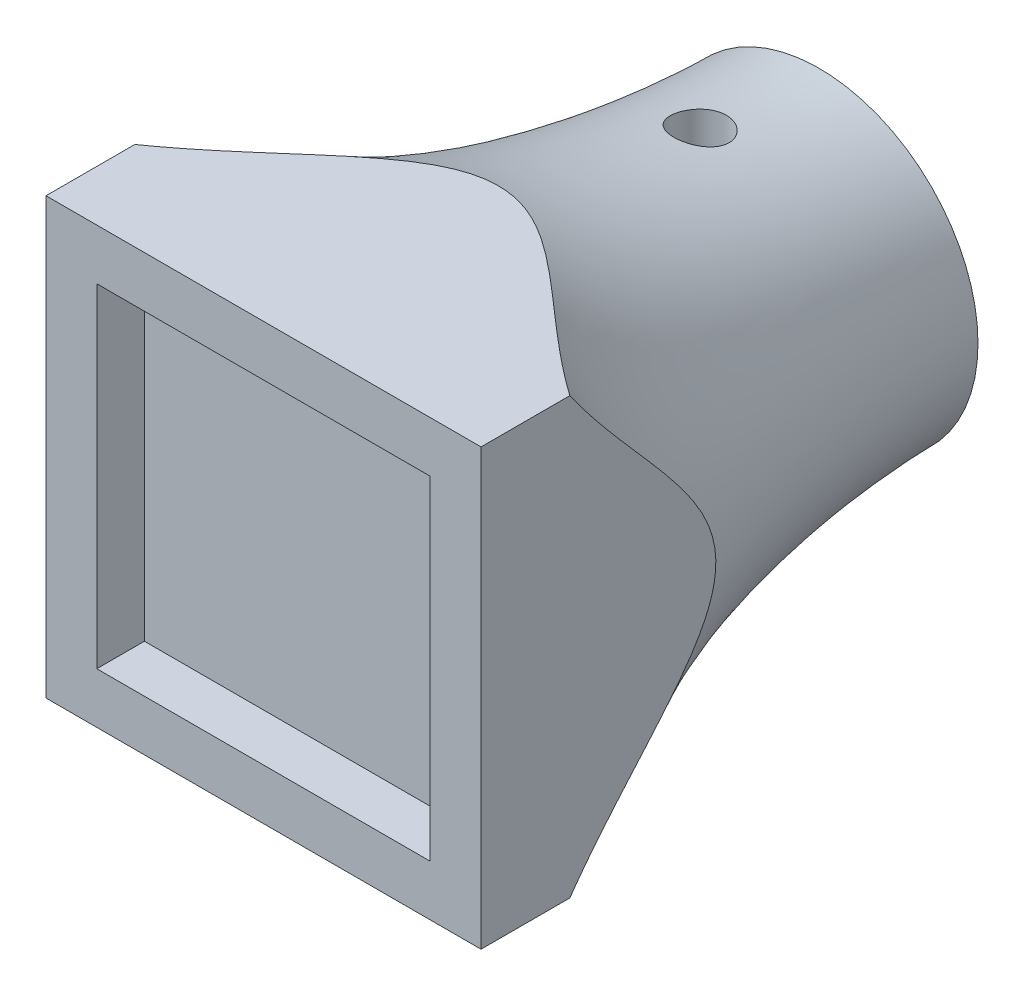
SolidWorks part; units mm, degrees
ref_plane "Front Plane" through (0, 0, 0) normal (0, 0, 1) x (1, 0, 0)
ref_plane "Top Plane" through (0, 0, 0) normal (0, 1, 0) x (1, 0, 0)
ref_plane "Right Plane" through (0, 0, 0) normal (1, 0, 0) x (0, 0, -1)
sketch "Sketch1" plane through (0, 0, 0) normal (0, 0, 1) x (1, 0, 0)
  circle A0 centre (0, 0) radius 10
  dimension "D1" = 20
extrude "Boss-Extrude1" add sketch "Sketch1" along normal blind 30
sketch "Sketch2" plane through (0, 0, 30) normal (0, 0, 1) x (1, 0, 0)
  line L0 (13.7, 13.7) -> (-13.7, 13.7)
  line L1 (10.5, 10.5) -> (-10.5, 10.5) construction
  line L2 (10.5, 10.5) -> (10.5, -10.5) construction
  line L3 (10.5, -10.5) -> (-10.5, -10.5) construction
  line L4 (-10.5, 10.5) -> (-10.5, -10.5) construction
  line L5 (10.5, 10.5) -> (-10.5, -10.5) construction
  line L6 (10.5, -10.5) -> (-10.5, 10.5) construction
  line L7 (-13.7, 13.7) -> (-13.7, -13.7)
  line L8 (13.7, -13.7) -> (-13.7, -13.7)
  line L9 (13.7, 13.7) -> (13.7, -13.7)
  point P0 (0, 0)
  dimension "D1" = 21
  dimension "D2" = 21
  dimension "D3" = 3.2
extrude "Boss-Extrude2" add sketch "Sketch2" along normal blind 5
sketch "Sketch3" plane through (0, 0, 35) normal (0, 0, 1) x (1, 0, 0)
  line L1 (10.5, 10.5) -> (-10.5, 10.5)
  line L2 (10.5, 10.5) -> (10.5, -10.5)
  line L3 (10.5, -10.5) -> (-10.5, -10.5)
  line L4 (-10.5, 10.5) -> (-10.5, -10.5)
  line L5 (10.5, 10.5) -> (-10.5, -10.5) construction
  line L6 (10.5, -10.5) -> (-10.5, 10.5) construction
  point P0 (0, 0)
  dimension "D1" = 21
  dimension "D2" = 21
extrude "Cut-Extrude1" cut sketch "Sketch3" against normal blind 3
sketch "Sketch5" plane through (0, 0, 0) normal (1, 0, 0) x (0, 0, -1)
  line L0 (-63.5412, 0) -> (-78.0067, 0)
sketch "Sketch6" plane through (0, 0, 0) normal (1, 0, 0) x (0, 0, -1)
  line L0 (-30, 0) -> (-30, 20)
  line L1 (-30, -13.7) -> (-30, 13.7) construction
  line L2 (-30, 0) -> (0, 0)
  line L3 (0, 0) -> (0, 10)
  line L4 (18.8276, 10) -> (-18.8276, 10) construction
  spline S0 degree 3 poles (-30, 20) (-22.0999, 11.2486) (-4.6132, 10) (0, 10) knots 0 0 0 0 1 1 1 1
  dimension "D1" = 20
revolve "Revolve1" add sketch "Sketch6" angle 360 about L0
sketch "Sketch7" plane through (0, 0, 30) normal (0, 0, 1) x (1, 0, 0)
  line L1 (13.7, 13.7) -> (-13.7, 13.7)
  line L2 (13.7, 13.7) -> (13.7, -13.7)
  line L3 (13.7, -13.7) -> (-13.7, -13.7)
  line L4 (-13.7, 13.7) -> (-13.7, -13.7)
  line L5 (13.7, 13.7) -> (-13.7, -13.7) construction
  line L6 (13.7, -13.7) -> (-13.7, 13.7) construction
  line L7 (23.5697, 23.5697) -> (-23.5697, 23.5697)
  line L8 (23.5697, 23.5697) -> (23.5697, -23.5697)
  line L9 (23.5697, -23.5697) -> (-23.5697, -23.5697)
  line L10 (-23.5697, 23.5697) -> (-23.5697, -23.5697)
  line L11 (23.5697, 23.5697) -> (-23.5697, -23.5697) construction
  line L12 (23.5697, -23.5697) -> (-23.5697, 23.5697) construction
  point P0 (0, 0)
  point P7 (0, 0)
extrude "Cut-Extrude2" cut sketch "Sketch7" against normal blind 78
sketch "Sketch8" plane through (0, 0, 0) normal (0, 0, -1) x (-1, 0, 0)
  line L0 (-1.6163, 2.1) -> (1.6163, 2.1)
  arc A0 (-1.6163, 2.1) -> (1.6163, 2.1) centre (0, 0) ccw
  dimension "D1" = 5.3
  dimension "D2" = 2.1
extrude "Cut-Extrude3" cut sketch "Sketch8" against normal blind 15
sketch "Sketch10" plane through (0, 2.1, 0) normal (0, -1, 0) x (1, 0, 0)
  line L0 (-10, 0) -> (10, 0) construction
  line L4 (0, 4.0359) -> (3, 5.7679)
  line L5 (3, 5.7679) -> (3, 9.2321)
  line L6 (3, 9.2321) -> (0, 10.9641)
  line L8 (-15.102, 10.9641) -> (0, 10.9641)
  line L9 (-15.102, 10.9641) -> (-15.102, 4.0359)
  line L10 (-15.102, 4.0359) -> (0, 4.0359)
  line L12 (-15.102, 10.9641) -> (0, 4.0359) construction
  line L13 (-15.102, 4.0359) -> (0, 10.9641) construction
  line L14 (0, 10.9641) -> (-3, 9.2321) [skipped]
  line L15 (-3, 9.2321) -> (-3, 5.7679) [skipped]
  line L16 (-3, 5.7679) -> (0, 4.0359) [skipped]
  circle A0 centre (0, 7.5) radius 3 construction
  point P11 (-7.551, 7.5)
  dimension "D1" = 6
  dimension "D2" = 0
  dimension "D3" = 7.5
extrude "Cut-Extrude4" cut sketch "Sketch10" against normal blind 3
sketch "Sketch11" plane through (0, 5.1, 0) normal (0, -1, 0) x (1, 0, 0)
  circle A0 centre (0, 7.5) radius 1.65
  dimension "D2" = 3.3
  dimension "D1" = 7.5
extrude "Cut-Extrude5" cut sketch "Sketch11" against normal blind 12
